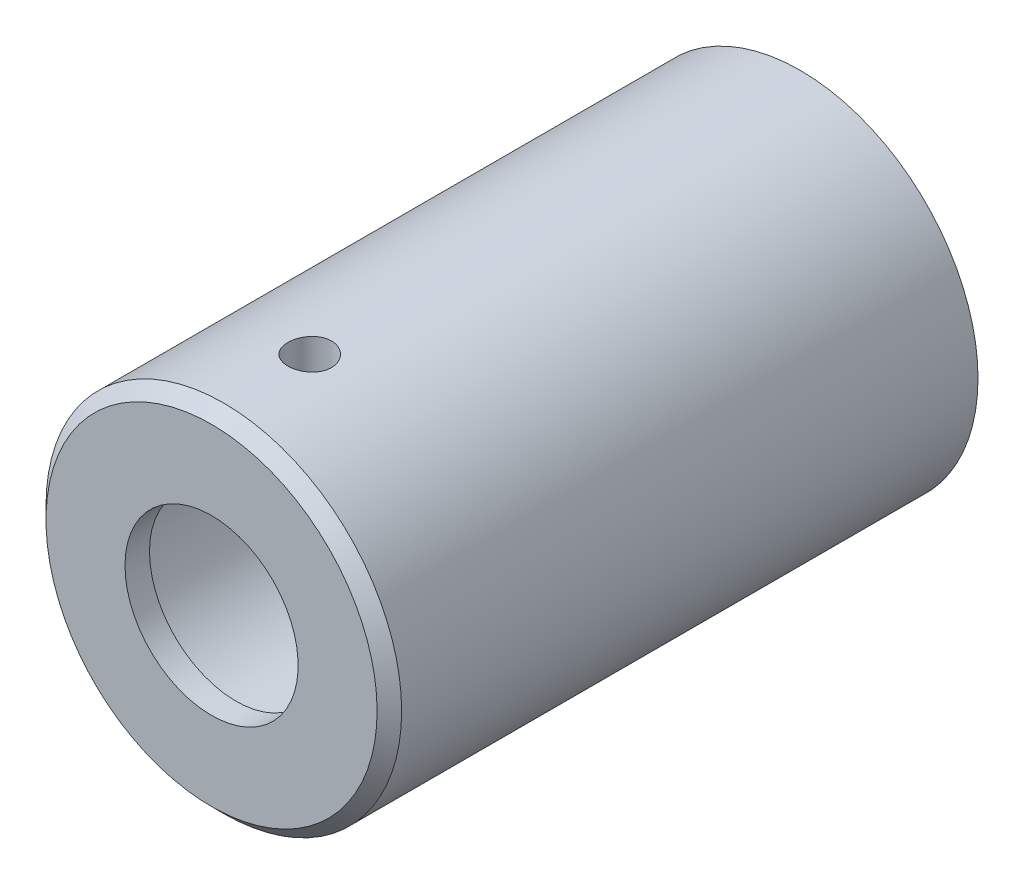
SolidWorks part; units mm, degrees
material "6061-T6 (SS)"
ref_plane "Front Plane" through (0, 0, 0) normal (0, 0, 1) x (1, 0, 0)
ref_plane "Top Plane" through (0, 0, 0) normal (0, 1, 0) x (1, 0, 0)
ref_plane "Right Plane" through (0, 0, 0) normal (1, 0, 0) x (0, 0, -1)
sketch "Sketch1" plane through (0, 0, 0) normal (1, 0, 0) x (0, 0, -1)
  line L0 (0, 0) -> (-37.4531, 0) construction
  line L1 (0, 7.25) -> (0, 3.53)
  line L2 (0, 3.53) -> (1, 3.53)
  line L3 (1, 3.53) -> (1, 4.53)
  line L4 (1, 4.53) -> (24, 4.53)
  line L6 (24, 7.25) -> (0, 7.25)
  line L8 (24, 4.53) -> (24, 7.25)
  dimension "D1" = 9.06
  dimension "D2" = 1
  dimension "D3" = 1
  dimension "D6" = 14.5
  dimension "D7" = 24
revolve "Revolve1" add sketch "Sketch1" angle 360 about L0
ref_plane "Plane1" through (0, 0, -4) normal (0, 0, -1) x (-1, 0, 0)
sketch "Sketch3" plane through (0, 0, -4) normal (0, 0, -1) x (-1, 0, 0)
  line L0 (0, 0) -> (0, 14.8228) construction
hole_wizard "#2-56 Tapped Hole2" positions "3DSketch2" profile "Sketch4" tap size "#2-56" standard "Ansi Inch"
sketch3d "3DSketch2"
  line L0 (0, 0, -4) -> (0, 14.8228, -4) construction
  point P0 (0, 7.25, -4)
sketch "Sketch4" plane through (0, 7.25, -4) normal (1, 0, 0) x (0, 0, 1)
  line L0 (0, 0) -> (0, 2.72)
  line L1 (0, 2.72) -> (0.889, 2.72)
  line L2 (0.889, 2.72) -> (0.889, 0)
  line L5 (0.889, 0) -> (0, 0)
  line L11 (0, -6.35) -> (0, 107.95) construction
  dimension "Thru Tap Drill Dia." = 1.778
  dimension "Thru Tap Drill Depth" = 2.72
cosmetic thread "Hole Thread2" parameters "D2"=2.1844
chamfer "Chamfer1" distance 0.5 angle 45 1 edges at (-7.25, 0, 0)
